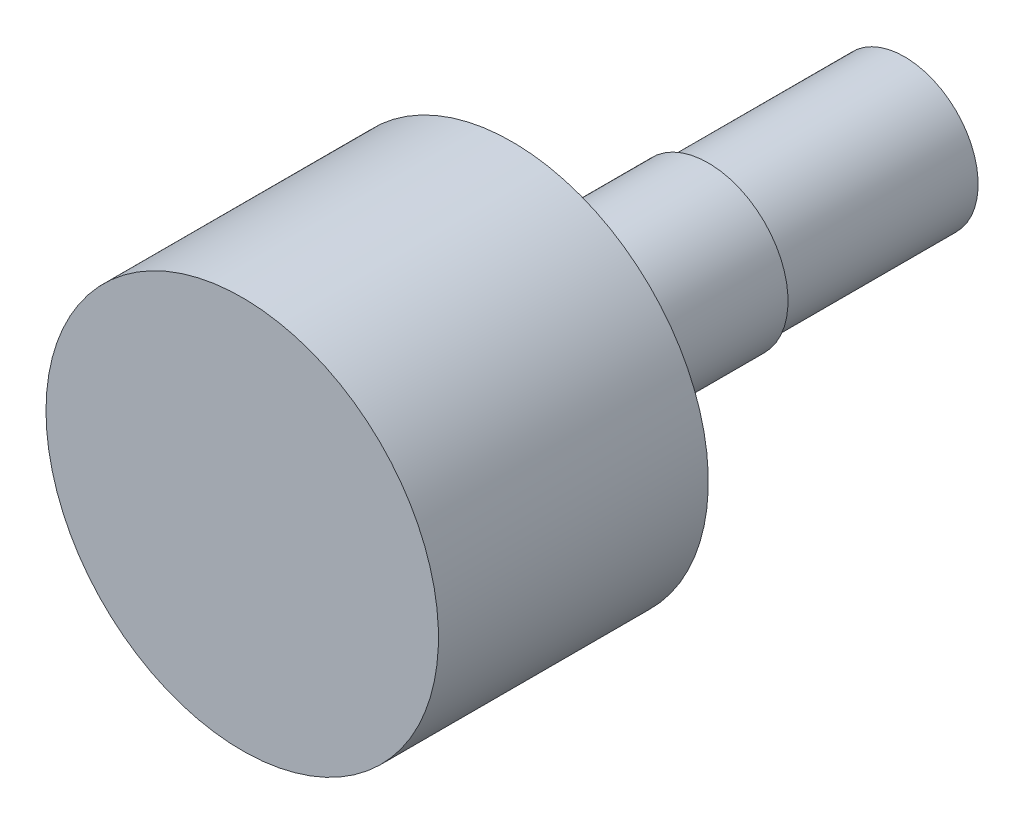
SolidWorks part; units mm, degrees
ref_plane "Front Plane" through (0, 0, 0) normal (0, 0, 1) x (1, 0, 0)
ref_plane "Top Plane" through (0, 0, 0) normal (0, 1, 0) x (1, 0, 0)
ref_plane "Right Plane" through (0, 0, 0) normal (1, 0, 0) x (0, 0, -1)
sketch "Sketch1" plane through (0, 0, 0) normal (1, 0, 0) x (0, 0, -1)
  line L0 (0, 0) -> (0, 8)
  line L1 (0, 8) -> (11, 8)
  line L2 (11, 8) -> (11, 3.25)
  line L3 (11, 3.25) -> (19, 3.25)
  line L4 (19, 3.25) -> (19, 3)
  line L5 (19, 3) -> (27, 3)
  line L6 (27, 3) -> (27, 0)
  line L7 (27, 0) -> (0, 0)
  line L8 (0, 0) -> (-12.7973, 0) construction
  dimension "D1" = 11
  dimension "D2" = 16
  dimension "D3" = 6.5
  dimension "D4" = 6
  dimension "D5" = 16
  dimension "D6" = 8
revolve "Revolve1" add sketch "Sketch1" angle 360 about L8
